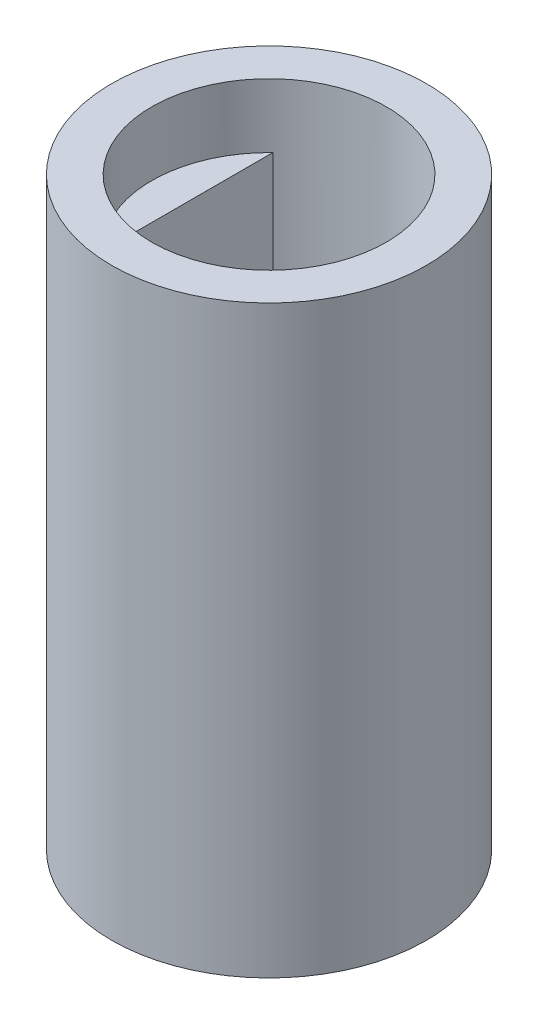
SolidWorks part; units mm, degrees
ref_plane "Front Plane" through (0, 0, 0) normal (0, 0, 1) x (1, 0, 0)
ref_plane "Top Plane" through (0, 0, 0) normal (0, 1, 0) x (1, 0, 0)
ref_plane "Right Plane" through (0, 0, 0) normal (1, 0, 0) x (0, 0, -1)
sketch "Sketch4" plane through (0, 0, 0) normal (0, 1, 0) x (1, 0, 0)
  circle A0 centre (-30.5561, -14.6857) radius 3.69
  dimension "D1" = 7.38
extrude "Boss-Extrude2" add sketch "Sketch4" along normal blind 13.7
sketch "Sketch5" plane through (0, 13.7, 0) normal (0, 1, 0) x (1, 0, 0)
  circle A0 centre (-30.5561, -14.6857) radius 2.75
  circle A1 centre (-30.5561, -14.6857) radius 3.69 construction
  dimension "D1" = 5.5
  dimension "D2" = 0
extrude "Cut-Extrude2" cut sketch "Sketch5" against normal blind 1.5
sketch "Sketch6" plane through (0, 12.2, 0) normal (0, 1, 0) x (1, 0, 0)
  line L1 (-28.6561, -19.6857) -> (-27.6561, -19.6857)
  line L2 (-28.6561, -19.6857) -> (-28.6561, -9.6857)
  line L3 (-28.6561, -9.6857) -> (-27.6561, -9.6857)
  line L4 (-27.6561, -19.6857) -> (-27.6561, -9.6857)
  line L5 (-32.4561, -19.6857) -> (-33.4561, -19.6857)
  line L6 (-32.4561, -19.6857) -> (-32.4561, -9.6857)
  line L7 (-32.4561, -9.6857) -> (-33.4561, -9.6857)
  line L8 (-33.4561, -19.6857) -> (-33.4561, -9.6857)
  circle A0 centre (-30.5561, -14.6857) radius 2.75
  circle A1 centre (-30.5561, -14.6857) radius 2.75 construction
  circle A2 centre (-30.5561, -14.6857) radius 3.69 construction
  circle M9 centre (-30.5561, -14.6857) radius 2.75
  dimension "D1" = 0
  dimension "D2" = 5.5
  dimension "D3" = 3.8
  dimension "D4" = 1
  dimension "D5" = 1
  dimension "D6" = 10
  dimension "D7" = 10
  dimension "D8" = 5
  dimension "D9" = 1.9
extrude "Cut-Extrude3" cut sketch "Sketch6" against normal blind 7.2 contours L6 L2 M9
sketch "Sketch7" plane through (0, 0, 0) normal (0, -1, 0) x (-1, 0, 0)
  line L1 (28.1061, -13.7357) -> (33.0061, -13.7357)
  line L2 (28.1061, -13.7357) -> (28.1061, -15.6357)
  line L3 (28.1061, -15.6357) -> (33.0061, -15.6357)
  line L4 (33.0061, -13.7357) -> (33.0061, -15.6357)
  line L5 (29.6061, -12.2357) -> (31.5061, -12.2357)
  line L6 (29.6061, -12.2357) -> (29.6061, -17.1357)
  line L7 (29.6061, -17.1357) -> (31.5061, -17.1357)
  line L8 (31.5061, -12.2357) -> (31.5061, -17.1357)
  circle A0 centre (30.5561, -14.6857) radius 3.69 construction
  dimension "D1" = 4.9
  dimension "D2" = 1.9
  dimension "D3" = 1.9
  dimension "D4" = 4.9
  dimension "D5" = 1.5
  dimension "D6" = 1.5
  dimension "D7" = 2.45
  dimension "D8" = 2.45
extrude "Cut-Extrude5" cut sketch "Sketch7" against normal blind 5 contours L8 L3 L6 L7 | L8 L1 L6 L3 | L6 L1 L2 L3 | L1 L8 L3 L4 | L8 L5 L6 L1
fillet "Fillet1" radius 0.75 1 edges at (-31.5061, 2.5, 15.6357)
fillet "Fillet2" radius 0.75 1 edges at (-29.6061, 2.5, 13.7357)
fillet "Fillet3" radius 0.75 1 edges at (-29.6061, 2.5, 15.6357)
fillet "Fillet4" radius 0.75 1 edges at (-31.5061, 2.5, 13.7357)
